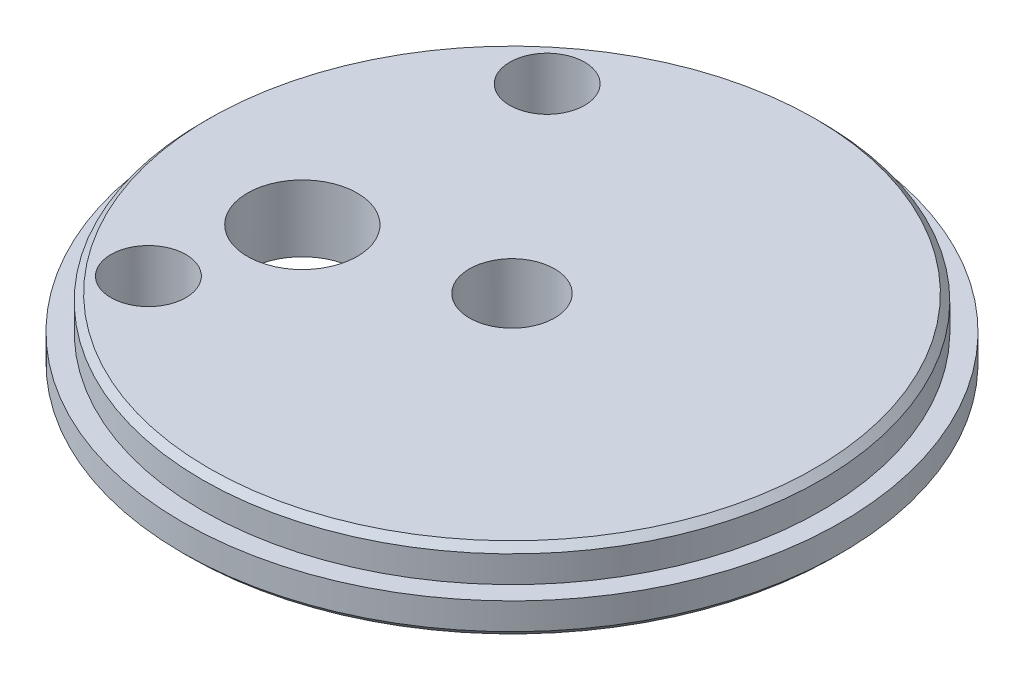
SolidWorks part; units mm, degrees
material "6061-T6 (SS)"
ref_plane "Front Plane" through (0, 0, 0) normal (0, 0, 1) x (1, 0, 0)
ref_plane "Top Plane" through (0, 0, 0) normal (0, 1, 0) x (1, 0, 0)
ref_plane "Right Plane" through (0, 0, 0) normal (1, 0, 0) x (0, 0, -1)
sketch "Sketch1" plane through (0, 0, 0) normal (0, 1, 0) x (1, 0, 0)
  circle A0 centre (0, 0) radius 25.146
  dimension "D1" = 50.292
extrude "Boss-Extrude1" add sketch "Sketch1" along normal blind 2.54
sketch "Sketch2" plane through (0, 2.54, 0) normal (0, 1, 0) x (1, 0, 0)
  circle A0 centre (0, 0) radius 23.622
  dimension "D1" = 47.244
extrude "Boss-Extrude2" add sketch "Sketch2" along normal blind 2.54
sketch "Sketch3" plane through (0, 0, 0) normal (0, -1, 0) x (1, 0, 0)
  circle A0 centre (0, 0) radius 3.2512
  circle A3 centre (-12.5377, 3.46) radius 4.191
  dimension "D1" = 6.5024
  dimension "D2" = 8.382
extrude "Cut-Extrude1" cut sketch "Sketch3" against normal through all and the other way through all
sketch "Sketch4" plane through (0, 0, 0) normal (0, -1, 0) x (1, 0, 0)
  circle A0 centre (-12.5126, -15.1965) radius 2.8575
  circle A1 centre (-15.019, 12.7251) radius 2.8575
  circle A2 centre (0, 0) radius 19.685 construction
  dimension "D1" = 5.715
extrude "Cut-Extrude2" cut sketch "Sketch4" against normal up to surface (5.08 mm away) up to face at (0, 5.08, -3.2512)
chamfer "Chamfer1" distance 0.508 angle 45 2 edges at (0, 0, 25.146) (0, 5.08, 23.622)
